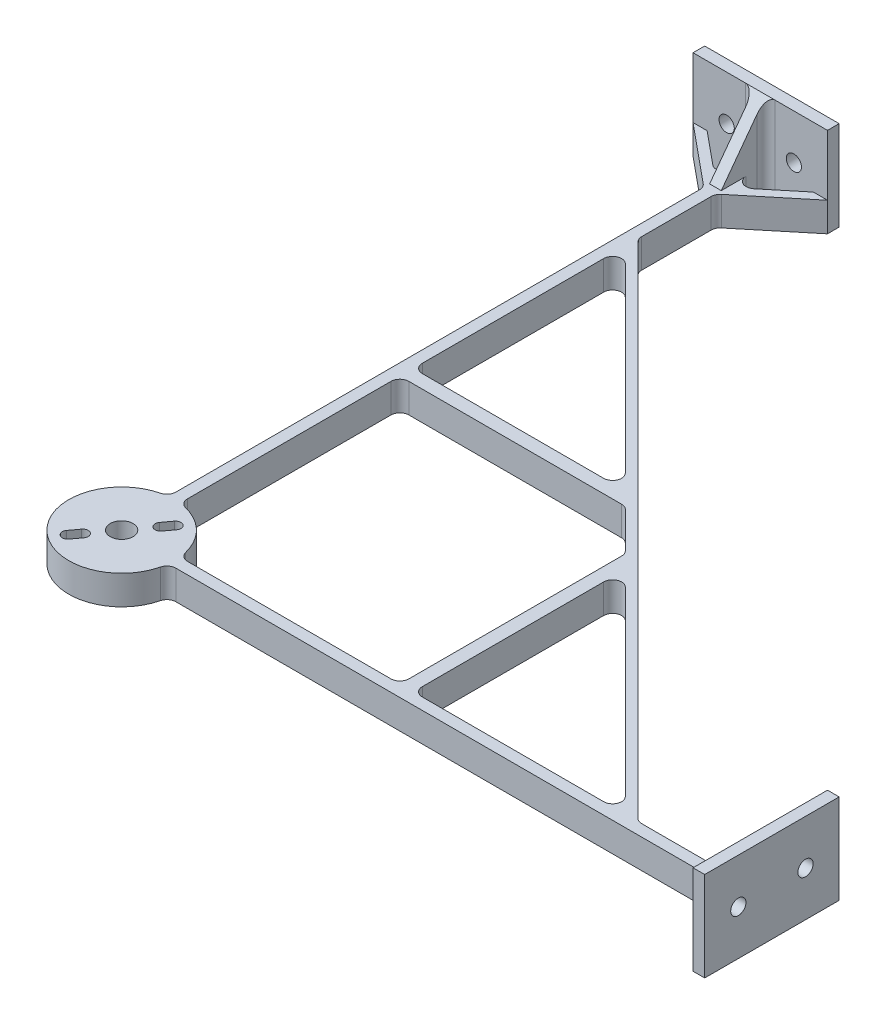
SolidWorks part; units mm, degrees
ref_plane "Front Plane" through (0, 0, 0) normal (0, 0, 1) x (1, 0, 0)
ref_plane "Top Plane" through (0, 0, 0) normal (0, 1, 0) x (1, 0, 0)
ref_plane "Right Plane" through (0, 0, 0) normal (1, 0, 0) x (0, 0, -1)
sketch "Sketch1" plane through (0, 0, 0) normal (0, 1, 0) x (1, 0, 0)
  line L0 (1.651, 14.8948) -> (1.651, 77.2021)
  line L1 (0, 0) -> (0, 189.2633) construction
  line L2 (-1.651, 14.8948) -> (-1.651, 180.975)
  line L3 (-1.651, 180.975) -> (1.651, 180.975)
  line L4 (-12.33, -16.663) -> (12.0176, 16.2408) construction
  line L5 (14.8948, -1.651) -> (180.975, -1.651)
  line L6 (4.6836, 6.3296) -> (6.4967, 8.7797) construction
  line L7 (3.4586, 7.2361) -> (5.2716, 9.6862)
  line L8 (180.975, -1.651) -> (180.975, 1.651)
  line L9 (14.8948, 1.651) -> (141.0789, 1.651)
  line L10 (5.9087, 5.4231) -> (7.7217, 7.8732)
  line L11 (0, 0) -> (16.238, -12.0155) construction
  line L12 (-4.6836, -6.3296) -> (-6.4967, -8.7797) construction
  line L13 (-5.9087, -5.4231) -> (-7.7217, -7.8732)
  line L14 (-3.4586, -7.2361) -> (-5.2716, -9.6862)
  line L15 (-1.651, 14.8948) -> (14.8948, -1.651) construction
  line L16 (1.651, 141.0789) -> (61.7178, 81.0121)
  line L17 (144.6711, 1.651) -> (1.651, 144.6711)
  line L18 (144.6711, 1.651) -> (166.629, 1.651)
  line L19 (141.0789, 1.651) -> (144.6711, 1.651) construction
  line L20 (1.651, 144.6711) -> (1.651, 180.975)
  line L21 (1.651, 81.0121) -> (61.7178, 81.0121)
  line L22 (1.651, 77.2021) -> (65.5278, 77.2021)
  line L23 (0, 0) -> (69.7604, 69.7604) construction
  line L24 (77.2021, 1.651) -> (77.2021, 65.5278)
  line L25 (81.0121, 1.651) -> (81.0121, 61.7178)
  line L26 (81.0121, 61.7178) -> (141.0789, 1.651)
  line L27 (65.5278, 77.2021) -> (77.2021, 65.5278)
  line L28 (1.651, 81.0121) -> (1.651, 141.0789)
  line L29 (169.921, 1.651) -> (180.975, 15.0573)
  line L30 (180.975, 15.0573) -> (180.975, 19.05)
  line L31 (180.975, 19.05) -> (166.629, 1.651)
  line L32 (166.4345, 0) -> (201.9953, 0) construction
  line L33 (180.975, -19.05) -> (166.629, -1.651)
  line L34 (180.975, -15.0573) -> (180.975, -19.05)
  line L35 (169.921, -1.651) -> (180.975, -15.0573)
  line L36 (169.921, 1.651) -> (180.975, 1.651)
  line L37 (166.629, 1.651) -> (169.921, 1.651) construction
  line L38 (-15.0573, 180.975) -> (-19.05, 180.975)
  line L39 (-19.05, 180.975) -> (-1.651, 166.629)
  line L40 (-1.651, 169.921) -> (-15.0573, 180.975)
  line L41 (1.651, 169.921) -> (15.0573, 180.975)
  line L42 (15.0573, 180.975) -> (19.05, 180.975)
  line L43 (19.05, 180.975) -> (1.651, 166.629)
  arc A0 (14.8948, 1.651) -> (1.651, 14.8948) centre (0, 0) ccw
  circle A1 centre (0, 0) radius 3.2385
  arc A2 (3.4586, 7.2361) -> (5.9087, 5.4231) centre (4.6836, 6.3296) ccw
  arc A3 (7.7217, 7.8732) -> (5.2716, 9.6862) centre (6.4967, 8.7797) ccw
  arc A4 (-5.9087, -5.4231) -> (-3.4586, -7.2361) centre (-4.6836, -6.3296) cw
  arc A5 (-5.2716, -9.6862) -> (-7.7217, -7.8732) centre (-6.4967, -8.7797) cw
  arc A6 (-1.651, 14.8948) -> (14.8948, -1.651) centre (0, 0) ccw
  point P14 (5.5901, 7.5546)
  point P25 (-5.5901, -7.5546)
  point P34 (142.875, 1.651)
  point P53 (168.275, 1.651)
  dimension "D3" = 29.972
  dimension "D1" = 6.477
  dimension "D6" = 1.524
  dimension "D7" = 3.048
  dimension "D2" = 36.5
  dimension "D4" = 3.302
  dimension "D5" = 3.302
  dimension "D8" = 7.874
  dimension "D9" = 2.54
  dimension "D10" = 38.1
  dimension "D11" = 3.81
  dimension "D12" = 16.51
  dimension "D13" = 38.1
  dimension "D14" = 12.7
  dimension "D15" = 2.54
  dimension "D16" = 180.975
  dimension "D17" = 180.975
extrude "Boss-Extrude1" add sketch "Sketch1" along normal blind 8.255
sketch "Sketch3" plane through (0, 0, 0) normal (0, 1, 0) x (1, 0, 0)
  line L0 (0, 0) -> (128.7769, 128.7769) construction
  line L1 (180.975, 19.05) -> (184.277, 19.05)
  line L2 (180.975, 19.05) -> (180.975, -19.05)
  line L3 (180.975, -19.05) -> (184.277, -19.05)
  line L4 (184.277, 19.05) -> (184.277, -19.05)
  line L5 (19.05, 184.277) -> (-19.05, 184.277)
  line L6 (-19.05, 180.975) -> (-19.05, 184.277)
  line L7 (19.05, 180.975) -> (-19.05, 180.975)
  line L8 (19.05, 180.975) -> (19.05, 184.277)
  dimension "D1" = 3.302
extrude "Boss-Extrude3" add sketch "Sketch3" along normal blind 25.4
sketch "Sketch4" plane through (0, 8.255, 0) normal (0, 1, 0) x (1, 0, 0)
  line L0 (65.2584, 81.0637) -> (64.3604, 80.1656)
  line L1 (144.6711, 1.651) -> (1.651, 144.6711) construction
  line L2 (64.3604, 80.1656) -> (80.1656, 64.3604)
  line L3 (80.1656, 64.3604) -> (81.0637, 65.2584)
  line L4 (81.0637, 65.2584) -> (65.2584, 81.0637)
  line L5 (71.365, 71.365) -> (72.263, 72.263) construction
  line L6 (65.5278, 77.2021) -> (77.2021, 65.5278) construction
  dimension "D1" = 22.352
  dimension "D2" = 1.27
extrude "Boss-Extrude4" [suppressed] add sketch "Sketch4" along normal blind 11.938
sketch "Sketch5" plane through (184.277, 0, 0) normal (1, 0, 0) x (0, 0, -1)
  line L0 (-19.05, 25.4) -> (19.05, 25.4) construction
  line L3 (0, 4.9298) -> (0, 30.0782) construction
  circle A0 centre (-9.525, 12.7) radius 2.159
  circle A1 centre (9.525, 12.7) radius 2.159
  dimension "D1" = 4.318
  dimension "D2" = 19.05
  dimension "D3" = 12.7
ref_plane "Plane1" [suppressed] through (0, 0, 0) normal (0.7071, 0, 0.7071) x (0.7071, 0, -0.7071)
extrude "Cut-Extrude1" cut sketch "Sketch5" against normal through all
mirror "Mirror1" about plane through (0, 0, 0) normal (0.7071, 0, 0.7071) of "Cut-Extrude1"
sketch "Sketch6" plane through (0, 0, 0) normal (0, 1, 0) x (1, 0, 0)
  line L0 (169.921, 1.651) -> (180.975, 1.651) construction
  line L1 (180.975, -1.651) -> (168.275, -1.651)
  line L2 (180.975, -1.651) -> (180.975, 1.651)
  line L3 (180.975, 1.651) -> (168.275, 1.651)
  line L4 (168.275, -1.651) -> (168.275, 1.651)
  dimension "D1" = 12.7
extrude "Boss-Extrude5" add sketch "Sketch6" along normal blind 25.4
sketch "Sketch7" plane through (0, 0, -1.651) normal (0, 0, -1) x (-1, 0, 0)
  line L0 (-180.975, 25.4) -> (-168.275, 8.255)
  line L1 (-168.275, 8.255) -> (-168.275, 25.4)
  line L2 (-168.275, 25.4) -> (-180.975, 25.4)
extrude "Cut-Extrude2" cut sketch "Sketch7" against normal blind 25.4
sketch "Sketch8" plane through (0, 0, 0) normal (0, 1, 0) x (1, 0, 0)
  line L0 (1.651, 169.921) -> (1.651, 180.975) construction
  line L1 (-1.651, 180.975) -> (1.651, 180.975)
  line L2 (-1.651, 180.975) -> (-1.651, 168.275)
  line L3 (-1.651, 168.275) -> (1.651, 168.275)
  line L4 (1.651, 180.975) -> (1.651, 168.275)
  dimension "D1" = 12.7
extrude "Boss-Extrude6" add sketch "Sketch8" along normal blind 25.4
sketch "Sketch9" plane through (1.651, 0, 0) normal (1, 0, 0) x (0, 0, -1)
  line L0 (180.975, 25.4) -> (168.275, 8.255)
  line L1 (168.275, 8.255) -> (168.275, 25.4)
  line L2 (168.275, 25.4) -> (180.975, 25.4)
extrude "Cut-Extrude3" cut sketch "Sketch9" against normal blind 25.4
fillet "Fillet1" radius 2.54 28 edges at (180.975, 12.7, 1.651) (-1.651, 12.7, -180.975) (141.0789, 4.1275, -1.651) (61.7178, 4.1275, -81.0121) (1.651, 4.1275, -141.0789) (81.0121, 4.1275, -61.7178) (14.8948, 4.1275, 1.651) (-1.651, 4.1275, -14.8948) (180.975, 12.7, -1.651) (77.2021, 4.1275, -1.651) (1.651, 12.7, -180.975) (1.651, 4.1275, -77.2021) (166.629, 4.1275, 1.651) (65.5278, 4.1275, -77.2021) (-1.651, 4.1275, -166.629) (77.2021, 4.1275, -65.5278) (1.651, 4.1275, -166.629) (1.651, 4.1275, -14.8948) (1.651, 4.1275, -144.6711) (1.651, 4.1275, -81.0121) (81.0121, 4.1275, -1.651) (166.629, 4.1275, -1.651) (14.8948, 4.1275, -1.651) (144.6711, 4.1275, -1.651) (1.651, 4.1275, -169.921) (-1.651, 4.1275, -169.921) (169.921, 4.1275, -1.651) (169.921, 4.1275, 1.651)
